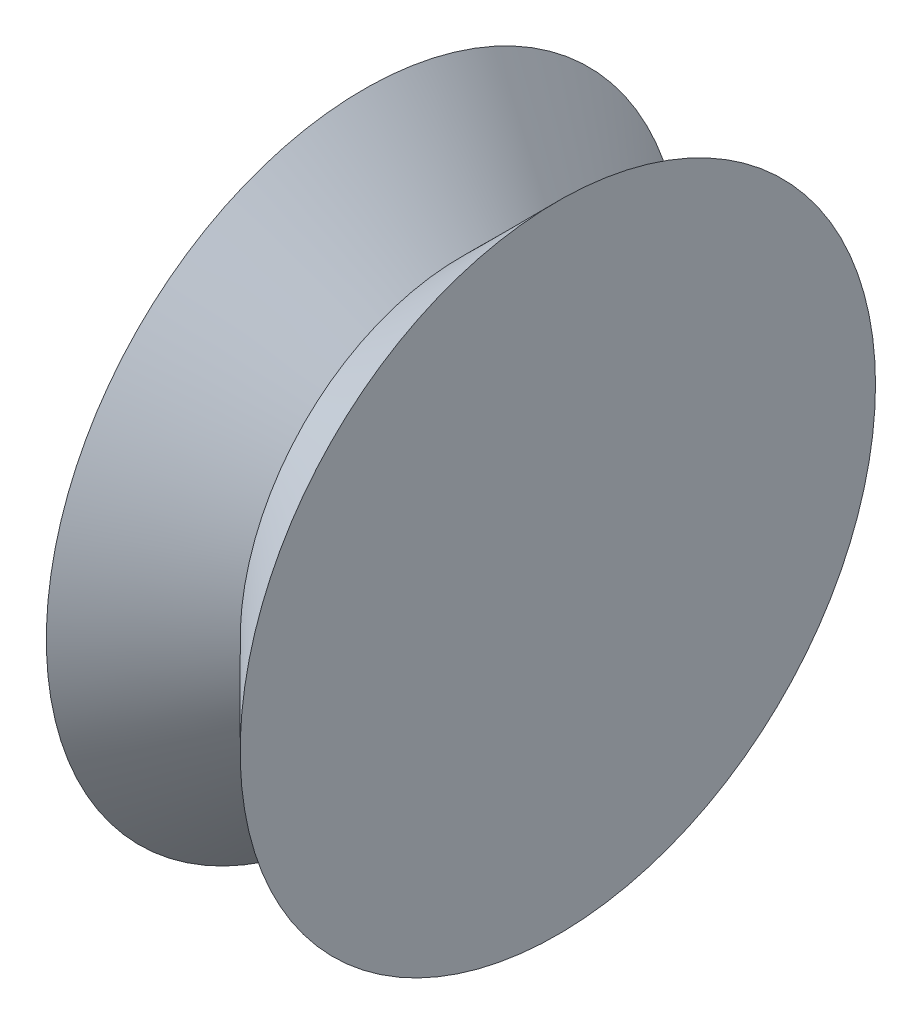
SolidWorks part; units mm, degrees
ref_plane "Front Plane" through (0, 0, 0) normal (0, 0, 1) x (1, 0, 0)
ref_plane "Top Plane" through (0, 0, 0) normal (0, 1, 0) x (1, 0, 0)
ref_plane "Right Plane" through (0, 0, 0) normal (1, 0, 0) x (0, 0, -1)
sketch "Sketch1" plane through (0, 0, 0) normal (0, 1, 0) x (1, 0, 0)
  line L0 (-5.6988, 5.4862) -> (-5.6988, -3.5138)
  line L1 (-5.6988, 5.4862) -> (-2.9528, 2.7402)
  line L2 (-2.9528, 2.7402) -> (-0.2067, 5.4862)
  line L3 (-0.2067, 5.4862) -> (-0.2067, -3.5138)
  line L4 (-0.2067, -3.5138) -> (-5.6988, -3.5138)
  dimension "D1" = 9
  dimension "D2" = 2.7461
  dimension "D3" = 5.4921
  dimension "D4" = 3.8835
revolve "Revolve1" add sketch "Sketch1" angle 360 about L4
